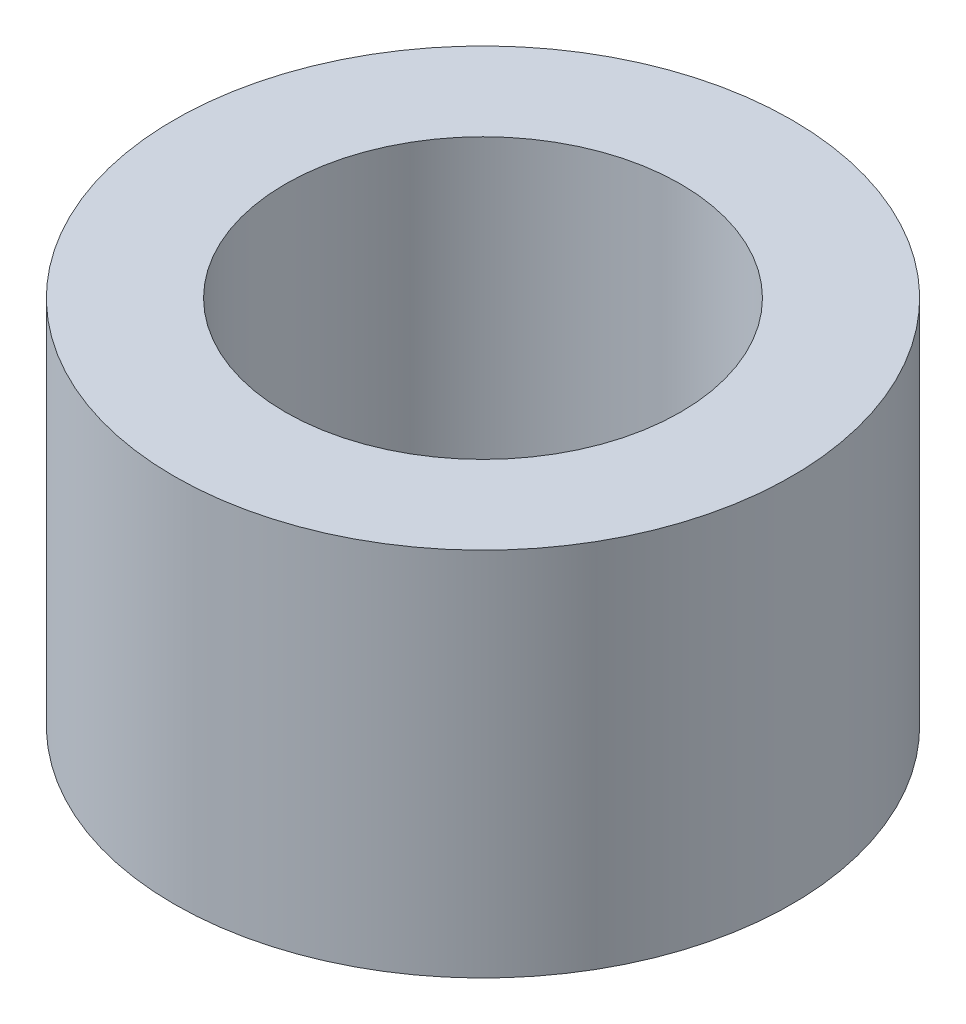
SolidWorks part; units mm, degrees
ref_plane "Front" through (0, 0, 0) normal (0, 0, 1) x (1, 0, 0)
ref_plane "Top" through (0, 0, 0) normal (0, 1, 0) x (1, 0, 0)
ref_plane "Right" through (0, 0, 0) normal (1, 0, 0) x (0, 0, -1)
sketch "Sketch1" plane through (0, 0, 0) normal (0, 1, 0) x (1, 0, 0)
  circle A0 centre (0, 0) radius 1.6
  circle A1 centre (0, 0) radius 2.5
  dimension "D1" = 5
  dimension "D2" = 3.2
extrude "Boss-Extrude1" add sketch "Sketch1" along normal blind 3
